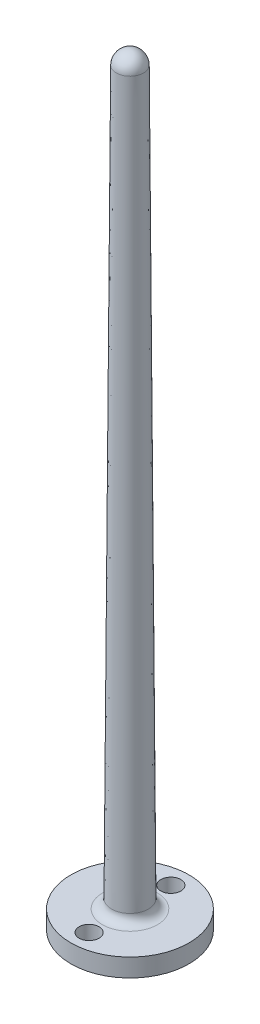
SolidWorks part; units mm, degrees
ref_plane "前视基准面" through (0, 0, 0) normal (0, 0, 1) x (1, 0, 0)
ref_plane "上视基准面" through (0, 0, 0) normal (0, 1, 0) x (1, 0, 0)
ref_plane "右视基准面" through (0, 0, 0) normal (1, 0, 0) x (0, 0, -1)
sketch "草图1" plane through (0, 0, 0) normal (0, 1, 0) x (1, 0, 0)
  circle A0 centre (0, 0) radius 6.5
  dimension "D1" = 13
extrude "凸台-拉伸1" add sketch "草图1" along normal blind 2
sketch "草图2" plane through (0, 2, 0) normal (0, 1, 0) x (1, 0, 0)
  line L0 (0, 0) -> (0, 3.7839) construction
  line L1 (0, 0) -> (3.1047, 0) construction
  circle A0 centre (0, 4.5) radius 1.1
  circle A1 centre (0, -4.5) radius 1.1
  dimension "D1" = 2.2
  dimension "D2" = 9
extrude "切除-拉伸1" cut sketch "草图2" against normal through all
sketch "草图3" plane through (0, 2, 0) normal (0, 1, 0) x (1, 0, 0)
  circle A0 centre (0, 0) radius 2.5
  dimension "D1" = 5
sketch "草图4" plane through (0, 0, 0) normal (0, 0, 1) x (1, 0, 0)
  line L0 (0, 2) -> (0, 82) construction
  line L1 (2.5, 2) -> (-2.5, 2) construction
  line L3 (1.5092, 81.5094) -> (2.0257, 2.9934)
  line L4 (3, 2) -> (0, 2)
  line L5 (6.5, 2) -> (-6.5, 2) construction
  line L6 (3.0257, 2) -> (3, 2)
  line L8 (1.503, 82.4453) -> (1.5092, 81.5094)
  line L9 (-0.403, 83.9384) -> (0.5001, 83.9384) construction
  line L10 (0, 83.9384) -> (0, 2)
  arc A1 (3.0257, 2) -> (2.0257, 2.9934) centre (3.0257, 3) cw
  arc A2 (0, 83.9384) -> (1.503, 82.4453) centre (0, 82.4354) cw
  point P0 (3.0257, 2)
  point P10 (1.503, 82.4453)
  dimension "D5" = 1
  dimension "D1" = 1.5031
  dimension "D2" = 3
revolve "旋转1" add sketch "草图4" angle 360 about L0
